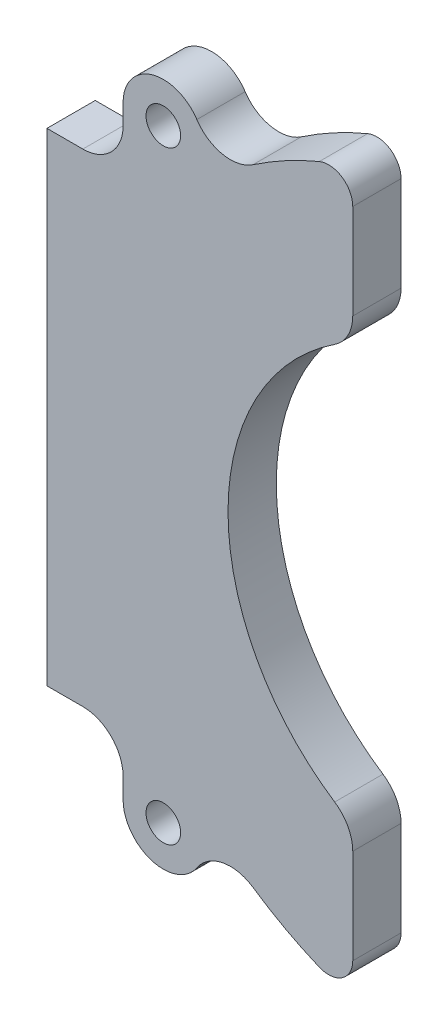
SolidWorks part; units mm, degrees
ref_plane "前视基准面" through (0, 0, 0) normal (0, 0, 1) x (1, 0, 0)
ref_plane "上视基准面" through (0, 0, 0) normal (0, 1, 0) x (1, 0, 0)
ref_plane "右视基准面" through (0, 0, 0) normal (1, 0, 0) x (0, 0, -1)
sketch "草图1" plane through (0, 0, 0) normal (0, 0, 1) x (1, 0, 0)
  line L0 (0, 0) -> (50000, 0) construction
  line L1 (-52, 8.75) -> (-52, -8.75)
  line L2 (-52, 8.75) -> (-52, 30)
  line L3 (-52, -8.75) -> (-52, -30)
  line L6 (-42.54, 37.5) -> (-42.54, 35)
  line L7 (-47.54, 30) -> (-52, 30)
  line L8 (-47.54, -30) -> (-52, -30)
  line L9 (-42.54, -37.5) -> (-42.54, -35)
  line L10 (0, 0) -> (0, -50000) construction
  line L11 (42.4995, 38.1352) -> (46.6192, 5.9711)
  line L12 (42.4995, -38.1352) -> (46.6192, -5.9711)
  circle A2 centre (-37.54, 37.5) radius 2.15
  circle A3 centre (-37.54, -37.5) radius 2.15
  arc A4 (-33.3722, 40.2622) -> (-42.54, 37.5) centre (-37.54, 37.5) ccw
  arc A5 (-42.54, -37.5) -> (-33.3722, -40.2622) centre (-37.54, -37.5) ccw
  arc A6 (-26.3963, -38.8874) -> (26.3963, -38.8874) centre (0, 0) ccw
  arc A7 (-33.3722, 40.2622) -> (-26.3963, 38.8874) centre (-29.2045, 43.0244) ccw
  arc A8 (-33.3722, -40.2622) -> (-42.54, -37.5) centre (-37.54, -37.5) cw
  arc A9 (-33.3722, -40.2622) -> (-26.3963, -38.8874) centre (-29.2045, -43.0244) cw
  circle A10 centre (37.54, -37.5) radius 2.15
  circle A11 centre (37.54, 37.5) radius 2.15
  arc A12 (42.4995, 38.1352) -> (33.3722, 40.2622) centre (37.54, 37.5) ccw
  arc A13 (33.3722, -40.2622) -> (42.4995, -38.1352) centre (37.54, -37.5) ccw
  arc A14 (33.3722, 40.2622) -> (26.3963, 38.8874) centre (29.2045, 43.0244) cw
  arc A15 (33.3722, -40.2622) -> (26.3963, -38.8874) centre (29.2045, -43.0244) ccw
  arc A16 (26.3963, 38.8874) -> (-26.3963, 38.8874) centre (0, 0) ccw
  arc A17 (46.6192, -5.9711) -> (46.6192, 5.9711) centre (0, 0) ccw
  arc A18 (-47.54, -30) -> (-42.54, -35) centre (-47.54, -35) cw
  arc A19 (-42.54, 35) -> (-47.54, 30) centre (-47.54, 35) cw
  point P8 (-52, 0)
  point P44 (-42.54, -30)
  point P47 (-42.54, 30)
  dimension "D5" = 4.3
  dimension "D6" = 75
  dimension "D8" = 10
  dimension "D9" = 94
  dimension "D10" = 5
  dimension "D11" = 10
  dimension "D12" = 5
  dimension "D13" = 5
  dimension "D14" = 5
  dimension "D2" = 17.5
  dimension "D3" = 52
  dimension "D4" = 60
  dimension "D7" = 14.46
extrude "凸台-拉伸1" add sketch "草图1" along normal blind 6
sketch "草图2" plane through (0, 0, 6) normal (0, 0, 1) x (1, 0, 0)
  line L0 (-14, 44.8665) -> (-14, 25.9663)
  line L1 (-14, -25.9663) -> (-14, -44.8665)
  line L7 (-42.54, 37.5) -> (-42.54, 35)
  line L8 (-47.54, 30) -> (-52, 30)
  line L9 (-52, 30) -> (-52, -30)
  line L10 (-52, -30) -> (-47.54, -30)
  line L11 (-42.54, -35) -> (-42.54, -37.5)
  line L12 (42.4995, -38.1352) -> (46.6192, -5.9711)
  line L13 (46.6192, 5.9711) -> (42.4995, 38.1352)
  line L19 (42.4995, -38.1352) -> (46.6192, -5.9711)
  line L20 (46.6192, 5.9711) -> (42.4995, 38.1352)
  arc A0 (-14, 25.9663) -> (-14, -25.9663) centre (0, 0) ccw
  arc A14 (-47.54, 30) -> (-42.54, 35) centre (-47.54, 35) ccw
  arc A15 (-42.54, -35) -> (-47.54, -30) centre (-47.54, -35) ccw
  arc A16 (-42.54, -37.5) -> (-33.3722, -40.2622) centre (-37.54, -37.5) ccw
  arc A17 (-26.3963, -38.8874) -> (-33.3722, -40.2622) centre (-29.2045, -43.0244) ccw
  arc A18 (-26.3963, -38.8874) -> (26.3963, -38.8874) centre (0, 0) ccw
  arc A19 (33.3722, -40.2622) -> (26.3963, -38.8874) centre (29.2045, -43.0244) ccw
  arc A20 (33.3722, -40.2622) -> (42.4995, -38.1352) centre (37.54, -37.5) ccw
  arc A21 (46.6192, -5.9711) -> (46.6192, 5.9711) centre (0, 0) ccw
  arc A22 (42.4995, 38.1352) -> (33.3722, 40.2622) centre (37.54, 37.5) ccw
  arc A23 (26.3963, 38.8874) -> (33.3722, 40.2622) centre (29.2045, 43.0244) ccw
  arc A24 (26.3963, 38.8874) -> (-26.3963, 38.8874) centre (0, 0) ccw
  arc A25 (-33.3722, 40.2622) -> (-26.3963, 38.8874) centre (-29.2045, 43.0244) ccw
  arc A26 (-33.3722, 40.2622) -> (-42.54, 37.5) centre (-37.54, 37.5) ccw
  arc A31 (-14, -44.8665) -> (26.3963, -38.8874) centre (0, 0) ccw
  arc A32 (33.3722, -40.2622) -> (26.3963, -38.8874) centre (29.2045, -43.0244) ccw
  arc A33 (33.3722, -40.2622) -> (42.4995, -38.1352) centre (37.54, -37.5) ccw
  arc A34 (46.6192, -5.9711) -> (46.6192, 5.9711) centre (0, 0) ccw
  arc A35 (42.4995, 38.1352) -> (33.3722, 40.2622) centre (37.54, 37.5) ccw
  arc A36 (26.3963, 38.8874) -> (33.3722, 40.2622) centre (29.2045, 43.0244) ccw
  arc A37 (26.3963, 38.8874) -> (-14, 44.8665) centre (0, 0) ccw
  dimension "D1" = 59
  dimension "D3" = 14
  dimension "D2" = 0
extrude "切除-拉伸1" cut sketch "草图2" against normal blind 10
fillet "圆角1" radius 5 2 edges at (-14, 25.9663, 3) (-14, -25.9663, 3)
fillet "圆角2" radius 3 2 edges at (-14, 44.8665, 3) (-14, -44.8665, 3)
